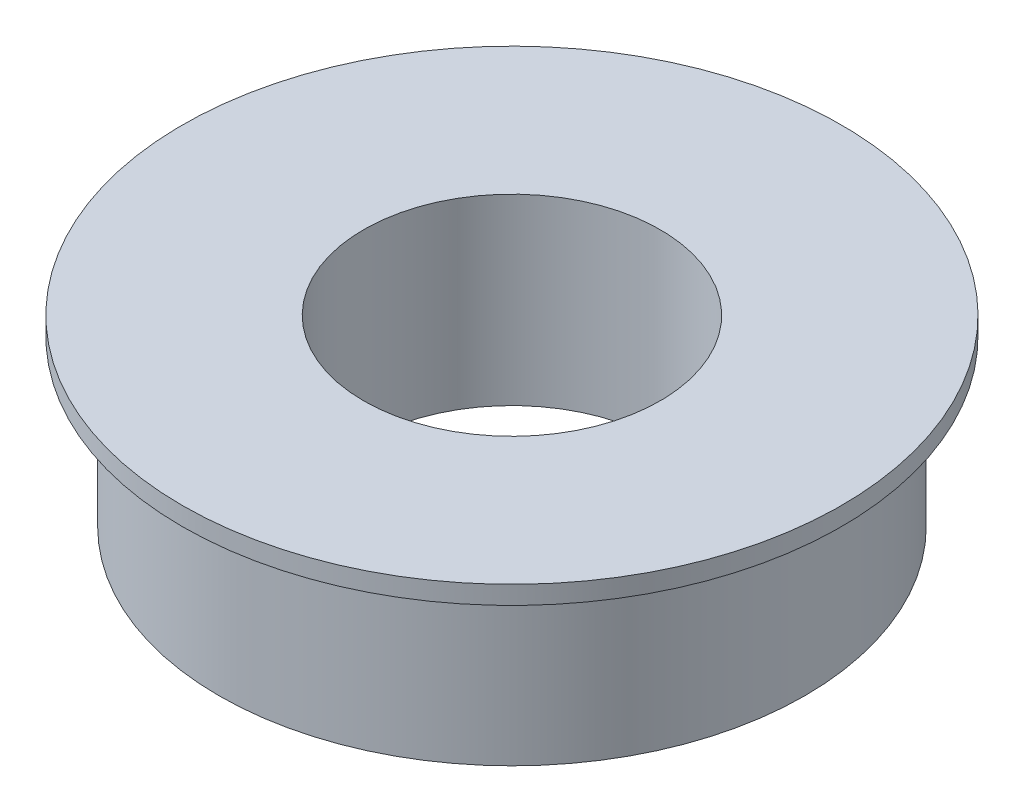
SolidWorks part; units mm, degrees
ref_plane "Front Plane" through (0, 0, 0) normal (0, 0, 1) x (1, 0, 0)
ref_plane "Top Plane" through (0, 0, 0) normal (0, 1, 0) x (1, 0, 0)
ref_plane "Right Plane" through (0, 0, 0) normal (1, 0, 0) x (0, 0, -1)
sketch "Sketch1" plane through (0, 0, 0) normal (0, 1, 0) x (1, 0, 0)
  circle A0 centre (0, 0) radius 8
  dimension "D1" = 16
extrude "Boss-Extrude1" add sketch "Sketch1" along normal blind 4.5
sketch "Sketch2" plane through (0, 4.5, 0) normal (0, 1, 0) x (1, 0, 0)
  circle A0 centre (0, 0) radius 9
  dimension "D1" = 18
extrude "Boss-Extrude2" add sketch "Sketch2" along normal blind 0.5
sketch "Sketch3" plane through (0, 5, 0) normal (0, 1, 0) x (1, 0, 0)
  circle A0 centre (0, 0) radius 4.05
  dimension "D1" = 8.1
extrude "Cut-Extrude1" cut sketch "Sketch3" against normal through all
